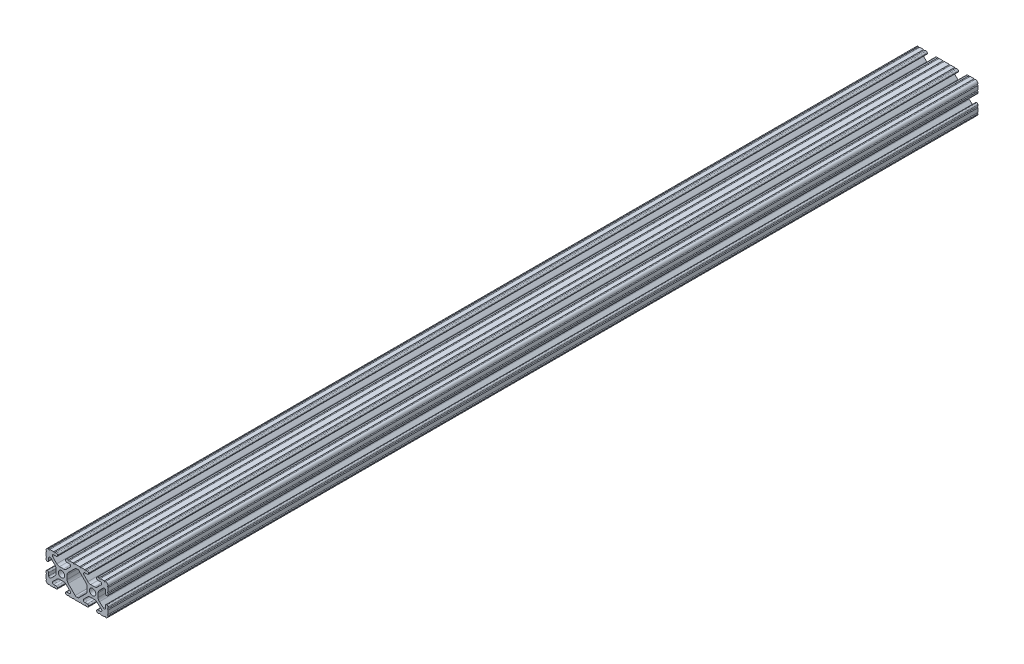
SolidWorks part; units mm, degrees
ref_plane "Front Plane" through (0, 0, 0) normal (0, 0, 1) x (1, 0, 0)
ref_plane "Top Plane" through (0, 0, 0) normal (0, 1, 0) x (1, 0, 0)
ref_plane "Right Plane" through (0, 0, 0) normal (1, 0, 0) x (0, 0, -1)
sketch "Sketch1" plane through (0, 0, 0) normal (0, 0, 1) x (1, 0, 0)
  line L0 (-7.2595, -3.8694) -> (-1.5457, -9.5728)
  line L1 (-8.1915, 1.6223) -> (-8.1915, -1.6223)
  line L2 (-1.504, 9.5765) -> (-7.252, 3.8768)
  line L3 (0.5515, 10.033) -> (-0.3952, 10.033)
  line L4 (7.2829, 3.8459) -> (1.6756, 9.5611)
  line L5 (8.1915, -1.6223) -> (8.1915, 1.6223)
  line L6 (1.5457, -9.5728) -> (7.2595, -3.8694)
  line L7 (-0.4332, -10.033) -> (0.4332, -10.033)
  line L8 (18.0171, 12.7) -> (16.9875, 12.7)
  line L9 (15.9385, 11.651) -> (15.9385, 11.5392)
  line L10 (16.9875, 10.4902) -> (19.1164, 10.4902)
  line L11 (19.8441, 8.7652) -> (16.619, 5.4551)
  line L12 (14.3449, 4.4958) -> (11.0833, 4.4958)
  line L13 (8.817, 5.4472) -> (5.5642, 8.7627)
  line L14 (6.2894, 10.4902) -> (8.4125, 10.4902)
  line L15 (9.4615, 11.5392) -> (9.4615, 11.651)
  line L16 (8.4125, 12.7) -> (7.3829, 12.7)
  line L17 (6.3669, 12.7) -> (3.1496, 12.7)
  line L18 (2.1336, 12.7) -> (-2.1336, 12.7)
  line L19 (-3.1496, 12.7) -> (-6.3669, 12.7)
  line L20 (-7.3829, 12.7) -> (-8.4125, 12.7)
  line L21 (-9.4615, 11.651) -> (-9.4615, 11.5392)
  line L22 (-8.4125, 10.4902) -> (-6.2836, 10.4902)
  line L23 (-5.5326, 8.6661) -> (-8.81, 5.4163)
  line L24 (-11.0455, 4.4958) -> (-14.3545, 4.4958)
  line L25 (-16.59, 5.4163) -> (-19.8674, 8.6661)
  line L26 (-19.1164, 10.4902) -> (-16.9875, 10.4902)
  line L27 (-15.9385, 11.5392) -> (-15.9385, 11.651)
  line L28 (-16.9875, 12.7) -> (-18.0171, 12.7)
  line L29 (-19.0331, 12.7) -> (-22.2504, 12.7)
  line L30 (-25.4, 9.5504) -> (-25.4, 6.3331)
  line L31 (-25.4, 5.3171) -> (-25.4, 4.2375)
  line L32 (-24.401, 3.2385) -> (-24.2392, 3.2385)
  line L33 (-23.1902, 4.2875) -> (-23.1902, 6.3347)
  line L34 (-21.434, 7.0665) -> (-18.148, 3.8082)
  line L35 (-17.2085, 1.5536) -> (-17.2085, -1.6952)
  line L36 (-18.1405, -3.9423) -> (-21.4316, -7.2274)
  line L37 (-23.1902, -6.498) -> (-23.1902, -4.2875)
  line L38 (-24.2392, -3.2385) -> (-24.351, -3.2385)
  line L39 (-25.4, -4.2875) -> (-25.4, -5.3171)
  line L40 (-25.4, -6.3331) -> (-25.4, -9.5504)
  line L41 (-22.2504, -12.7) -> (-19.0331, -12.7)
  line L42 (-18.0171, -12.7) -> (-16.9875, -12.7)
  line L43 (-15.9384, -11.651) -> (-15.9384, -11.5392)
  line L44 (-16.9875, -10.4902) -> (-19.1164, -10.4902)
  line L45 (-19.8341, -8.7551) -> (-16.4966, -5.4237)
  line L46 (-14.2536, -4.4958) -> (-11.1464, -4.4958)
  line L47 (-8.9034, -5.4237) -> (-5.5659, -8.7551)
  line L48 (-6.2836, -10.4902) -> (-8.4125, -10.4902)
  line L49 (-9.4616, -11.5392) -> (-9.4616, -11.651)
  line L50 (-8.4125, -12.7) -> (-7.3829, -12.7)
  line L51 (-6.3669, -12.7) -> (-3.1496, -12.7)
  line L52 (-2.1336, -12.7) -> (2.1336, -12.7)
  line L53 (3.1496, -12.7) -> (6.3669, -12.7)
  line L54 (7.3829, -12.7) -> (8.4125, -12.7)
  line L55 (9.4616, -11.651) -> (9.4616, -11.5392)
  line L56 (8.4125, -10.4902) -> (6.2894, -10.4902)
  line L57 (5.4807, -8.5353) -> (8.5979, -5.4237)
  line L58 (10.8409, -4.4958) -> (14.1026, -4.4958)
  line L59 (16.1879, -5.2766) -> (19.8682, -8.4822)
  line L60 (19.1164, -10.4902) -> (16.9875, -10.4902)
  line L61 (15.9384, -11.5392) -> (15.9384, -11.651)
  line L62 (16.9875, -12.7) -> (18.0171, -12.7)
  line L63 (19.0331, -12.7) -> (22.2504, -12.7)
  line L64 (25.4, -9.5504) -> (25.4, -6.3331)
  line L65 (25.4, -5.3171) -> (25.4, -4.2375)
  line L66 (24.401, -3.2385) -> (24.1892, -3.2385)
  line L67 (23.1902, -4.2375) -> (23.1902, -6.1559)
  line L68 (21.584, -6.8869) -> (18.2982, -4.025)
  line L69 (17.2085, -1.6308) -> (17.2085, 1.6308)
  line L70 (18.1094, 3.8465) -> (21.5263, 7.3534)
  line L71 (23.1902, 6.6769) -> (23.1902, 4.2375)
  line L72 (24.1892, 3.2385) -> (24.401, 3.2385)
  line L73 (25.4, 4.2375) -> (25.4, 5.3171)
  line L74 (25.4, 6.3332) -> (25.4, 9.5504)
  line L75 (22.2504, 12.7) -> (19.0331, 12.7)
  circle A0 centre (-12.7, 0) radius 2.6035
  circle A1 centre (12.7, 0) radius 2.6035
  arc A2 (-1.5457, -9.5728) -> (-0.4332, -10.033) centre (-0.4332, -8.4582) ccw
  arc A3 (-8.1915, -1.6223) -> (-7.2595, -3.8694) centre (-5.0165, -1.6223) ccw
  arc A4 (-7.252, 3.8768) -> (-8.1915, 1.6223) centre (-5.0165, 1.6223) ccw
  arc A5 (-0.3952, 10.033) -> (-1.504, 9.5765) centre (-0.3952, 8.4582) ccw
  arc A6 (1.6756, 9.5611) -> (0.5515, 10.033) centre (0.5515, 8.4582) ccw
  arc A7 (8.1915, 1.6223) -> (7.2829, 3.8459) centre (5.0165, 1.6223) ccw
  arc A8 (7.2595, -3.8694) -> (8.1915, -1.6223) centre (5.0165, -1.6223) ccw
  arc A9 (0.4332, -10.033) -> (1.5457, -9.5728) centre (0.4332, -8.4582) ccw
  arc A10 (18.0171, 12.7) -> (19.0331, 12.7) centre (18.5251, 12.7) ccw
  arc A11 (16.9875, 12.7) -> (15.9385, 11.651) centre (16.9875, 11.651) ccw
  arc A12 (15.9385, 11.5392) -> (16.9875, 10.4902) centre (16.9875, 11.5392) ccw
  arc A13 (19.8441, 8.7652) -> (19.1164, 10.4902) centre (19.1164, 9.4742) ccw
  arc A14 (14.3449, 4.4958) -> (16.619, 5.4551) centre (14.3449, 7.6708) ccw
  arc A15 (8.817, 5.4472) -> (11.0833, 4.4958) centre (11.0833, 7.6708) ccw
  arc A16 (6.2894, 10.4902) -> (5.5642, 8.7627) centre (6.2894, 9.4742) ccw
  arc A17 (8.4125, 10.4902) -> (9.4615, 11.5392) centre (8.4125, 11.5392) ccw
  arc A18 (9.4615, 11.651) -> (8.4125, 12.7) centre (8.4125, 11.651) ccw
  arc A19 (6.3669, 12.7) -> (7.3829, 12.7) centre (6.8749, 12.7) ccw
  arc A20 (2.1336, 12.7) -> (3.1496, 12.7) centre (2.6416, 12.7) ccw
  arc A21 (-3.1496, 12.7) -> (-2.1336, 12.7) centre (-2.6416, 12.7) ccw
  arc A22 (-7.3829, 12.7) -> (-6.3669, 12.7) centre (-6.8749, 12.7) ccw
  arc A23 (-8.4125, 12.7) -> (-9.4615, 11.651) centre (-8.4125, 11.651) ccw
  arc A24 (-9.4615, 11.5392) -> (-8.4125, 10.4902) centre (-8.4125, 11.5392) ccw
  arc A25 (-5.5326, 8.6661) -> (-6.2836, 10.4902) centre (-6.2836, 9.4235) ccw
  arc A26 (-11.0455, 4.4958) -> (-8.81, 5.4163) centre (-11.0455, 7.6708) ccw
  arc A27 (-16.59, 5.4163) -> (-14.3545, 4.4958) centre (-14.3545, 7.6708) ccw
  arc A28 (-19.1164, 10.4902) -> (-19.8674, 8.6661) centre (-19.1164, 9.4235) ccw
  arc A29 (-16.9875, 10.4902) -> (-15.9385, 11.5392) centre (-16.9875, 11.5392) ccw
  arc A30 (-15.9385, 11.651) -> (-16.9875, 12.7) centre (-16.9875, 11.651) ccw
  arc A31 (-19.0331, 12.7) -> (-18.0171, 12.7) centre (-18.5251, 12.7) ccw
  arc A32 (-23.2664, 12.6998) -> (-22.2504, 12.7) centre (-22.7584, 12.7) ccw
  arc A33 (-23.2664, 12.6998) -> (-25.3998, 10.5664) centre (-23.2918, 10.5918) ccw
  arc A34 (-25.4, 9.5504) -> (-25.3998, 10.5664) centre (-25.4, 10.0584) ccw
  arc A35 (-25.4, 5.3171) -> (-25.4, 6.3331) centre (-25.4, 5.8251) ccw
  arc A36 (-25.4, 4.2375) -> (-24.401, 3.2385) centre (-24.401, 4.2375) ccw
  arc A37 (-24.2392, 3.2385) -> (-23.1902, 4.2875) centre (-24.2392, 4.2875) ccw
  arc A38 (-21.434, 7.0665) -> (-23.1902, 6.3347) centre (-22.1596, 6.3347) ccw
  arc A39 (-17.2085, 1.5536) -> (-18.148, 3.8082) centre (-20.3835, 1.5536) ccw
  arc A40 (-18.1405, -3.9423) -> (-17.2085, -1.6952) centre (-20.3835, -1.6952) ccw
  arc A41 (-23.1902, -6.498) -> (-21.4316, -7.2274) centre (-22.1596, -6.498) ccw
  arc A42 (-23.1902, -4.2875) -> (-24.2392, -3.2385) centre (-24.2392, -4.2875) ccw
  arc A43 (-24.351, -3.2385) -> (-25.4, -4.2875) centre (-24.351, -4.2875) ccw
  arc A44 (-25.4, -6.3331) -> (-25.4, -5.3171) centre (-25.4, -5.8251) ccw
  arc A45 (-25.3998, -10.5664) -> (-25.4, -9.5504) centre (-25.4, -10.0584) ccw
  arc A46 (-25.3998, -10.5664) -> (-23.2664, -12.6998) centre (-23.2918, -10.5918) ccw
  arc A47 (-22.2504, -12.7) -> (-23.2664, -12.6998) centre (-22.7584, -12.7) ccw
  arc A48 (-18.0171, -12.7) -> (-19.0331, -12.7) centre (-18.5251, -12.7) ccw
  arc A49 (-16.9875, -12.7) -> (-15.9384, -11.651) centre (-16.9875, -11.651) ccw
  arc A50 (-15.9384, -11.5392) -> (-16.9875, -10.4902) centre (-16.9875, -11.5392) ccw
  arc A51 (-19.8341, -8.7551) -> (-19.1164, -10.4902) centre (-19.1164, -9.4742) ccw
  arc A52 (-14.2536, -4.4958) -> (-16.4966, -5.4237) centre (-14.2536, -7.6708) ccw
  arc A53 (-8.9034, -5.4237) -> (-11.1464, -4.4958) centre (-11.1464, -7.6708) ccw
  arc A54 (-6.2836, -10.4902) -> (-5.5659, -8.7551) centre (-6.2836, -9.4742) ccw
  arc A55 (-8.4125, -10.4902) -> (-9.4616, -11.5392) centre (-8.4125, -11.5392) ccw
  arc A56 (-9.4616, -11.651) -> (-8.4125, -12.7) centre (-8.4125, -11.651) ccw
  arc A57 (-6.3669, -12.7) -> (-7.3829, -12.7) centre (-6.8749, -12.7) ccw
  arc A58 (-2.1336, -12.7) -> (-3.1496, -12.7) centre (-2.6416, -12.7) ccw
  arc A59 (3.1496, -12.7) -> (2.1336, -12.7) centre (2.6416, -12.7) ccw
  arc A60 (7.3829, -12.7) -> (6.3669, -12.7) centre (6.8749, -12.7) ccw
  arc A61 (8.4125, -12.7) -> (9.4616, -11.651) centre (8.4125, -11.651) ccw
  arc A62 (9.4616, -11.5392) -> (8.4125, -10.4902) centre (8.4125, -11.5392) ccw
  arc A63 (5.4807, -8.5353) -> (6.2894, -10.4902) centre (6.2894, -9.3455) ccw
  arc A64 (10.8409, -4.4958) -> (8.5979, -5.4237) centre (10.8409, -7.6708) ccw
  arc A65 (16.1879, -5.2766) -> (14.1026, -4.4958) centre (14.1026, -7.6708) ccw
  arc A66 (19.1164, -10.4902) -> (19.8682, -8.4822) centre (19.1164, -9.3455) ccw
  arc A67 (16.9875, -10.4902) -> (15.9384, -11.5392) centre (16.9875, -11.5392) ccw
  arc A68 (15.9384, -11.651) -> (16.9875, -12.7) centre (16.9875, -11.651) ccw
  arc A69 (19.0331, -12.7) -> (18.0171, -12.7) centre (18.5251, -12.7) ccw
  arc A70 (23.2664, -12.6998) -> (22.2504, -12.7) centre (22.7584, -12.7) ccw
  arc A71 (23.2664, -12.6998) -> (25.3998, -10.5664) centre (23.2918, -10.5918) ccw
  arc A72 (25.4, -9.5504) -> (25.3998, -10.5664) centre (25.4, -10.0584) ccw
  arc A73 (25.4, -5.3171) -> (25.4, -6.3331) centre (25.4, -5.8251) ccw
  arc A74 (25.4, -4.2375) -> (24.401, -3.2385) centre (24.401, -4.2375) ccw
  arc A75 (24.1892, -3.2385) -> (23.1902, -4.2375) centre (24.1892, -4.2375) ccw
  arc A76 (21.584, -6.8869) -> (23.1902, -6.1559) centre (22.2207, -6.1559) ccw
  arc A77 (17.2085, -1.6308) -> (18.2982, -4.025) centre (20.3835, -1.6308) ccw
  arc A78 (18.1094, 3.8465) -> (17.2085, 1.6308) centre (20.3835, 1.6308) ccw
  arc A79 (23.1902, 6.6769) -> (21.5263, 7.3534) centre (22.2207, 6.6769) ccw
  arc A80 (23.1902, 4.2375) -> (24.1892, 3.2385) centre (24.1892, 4.2375) ccw
  arc A81 (24.401, 3.2385) -> (25.4, 4.2375) centre (24.401, 4.2375) ccw
  arc A82 (25.4, 6.3332) -> (25.4, 5.3171) centre (25.4, 5.8251) ccw
  arc A83 (25.3998, 10.5664) -> (25.4, 9.5504) centre (25.4, 10.0584) ccw
  arc A84 (25.3998, 10.5664) -> (23.2664, 12.6998) centre (23.2918, 10.5918) ccw
  arc A85 (22.2504, 12.7) -> (23.2664, 12.6998) centre (22.7584, 12.7) ccw
  point P248 (0, 10.033)
extrude "Boss-Extrude1" add sketch "Sketch1" along normal mid plane 711.2
